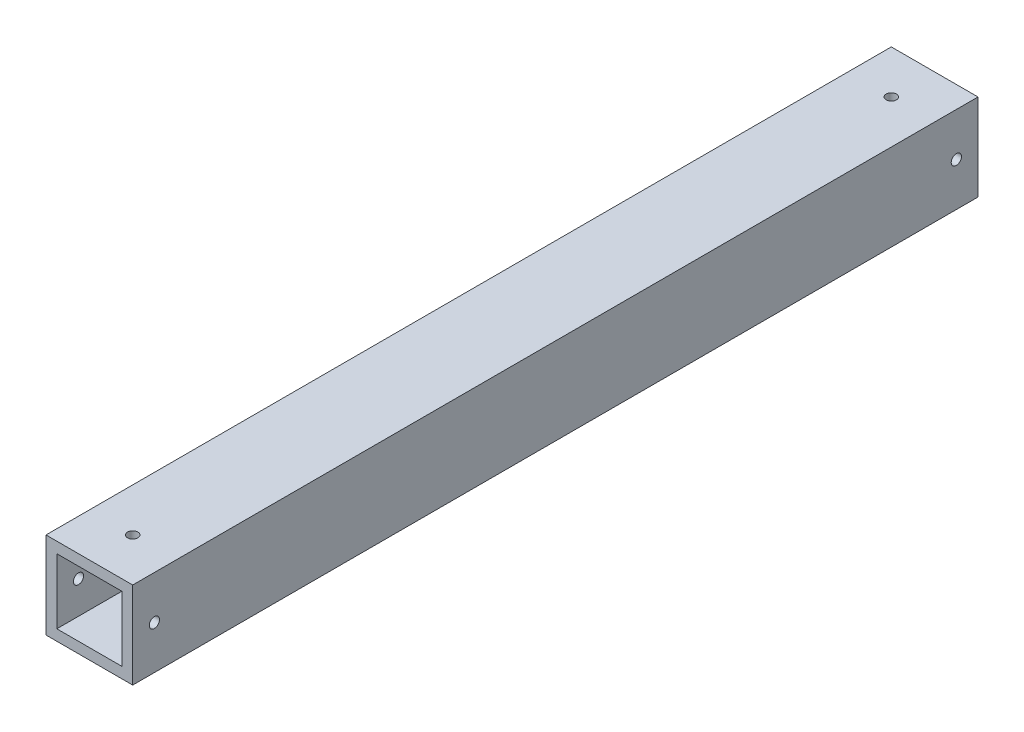
SolidWorks part; units mm, degrees
material "1060-O (SS)"
ref_plane "Front Plane" through (0, 0, 0) normal (0, 0, 1) x (1, 0, 0)
ref_plane "Top Plane" through (0, 0, 0) normal (0, 1, 0) x (1, 0, 0)
ref_plane "Right Plane" through (0, 0, 0) normal (1, 0, 0) x (0, 0, -1)
sketch "Sketch1" plane through (0, 0, 0) normal (0, 0, 1) x (1, 0, 0)
  line L1 (-12.7, -12.7) -> (12.7, -12.7)
  line L2 (-12.7, -12.7) -> (-12.7, 12.7)
  line L3 (-12.7, 12.7) -> (12.7, 12.7)
  line L4 (12.7, -12.7) -> (12.7, 12.7)
  line L5 (-12.7, -12.7) -> (12.7, 12.7) construction
  line L6 (-12.7, 12.7) -> (12.7, -12.7) construction
  line L7 (-9.525, -9.525) -> (9.525, -9.525)
  line L8 (-9.525, -9.525) -> (-9.525, 9.525)
  line L9 (-9.525, 9.525) -> (9.525, 9.525)
  line L10 (9.525, -9.525) -> (9.525, 9.525)
  line L11 (-9.525, -9.525) -> (9.525, 9.525) construction
  line L12 (-9.525, 9.525) -> (9.525, -9.525) construction
  point P0 (0, 0)
  point P5 (0, 0)
  dimension "D1" = 25.4
  dimension "D2" = 25.4
  dimension "D3" = 3.175
  dimension "D4" = 3.175
extrude "Boss-Extrude1" add sketch "Sketch1" along normal blind 247.65
sketch "Sketch2" plane through (12.7, 0, 0) normal (1, 0, 0) x (0, 0, -1)
  line L0 (-247.65, -12.7) -> (-247.65, 12.7) construction
  line L1 (0, -12.7) -> (0, 12.7) construction
  line L2 (-247.65, -12.7) -> (0, -12.7) construction
  circle A0 centre (-241.3, 0) radius 1.5
  circle A1 centre (-6.35, 0) radius 1.5
  dimension "D1" = 3
  dimension "D2" = 3
  dimension "D3" = 6.35
  dimension "D4" = 6.35
  dimension "D5" = 12.7
  dimension "D6" = 12.7
extrude "Cut-Extrude1" cut sketch "Sketch2" against normal blind 254
sketch "Sketch3" plane through (0, 12.7, 0) normal (0, 1, 0) x (1, 0, 0)
  line L0 (12.7, -247.65) -> (-12.7, -247.65) construction
  line L1 (12.7, -247.65) -> (12.7, 0) construction
  line L2 (12.7, 0) -> (-12.7, 0) construction
  circle A0 centre (0, -12.7) radius 1.5
  circle A1 centre (0, -234.95) radius 1.5
  dimension "D1" = 3
  dimension "D2" = 12.7
  dimension "D3" = 12.7
  dimension "D4" = 3
  dimension "D5" = 12.7
  dimension "D6" = 12.7
extrude "Cut-Extrude2" cut sketch "Sketch3" against normal blind 254
